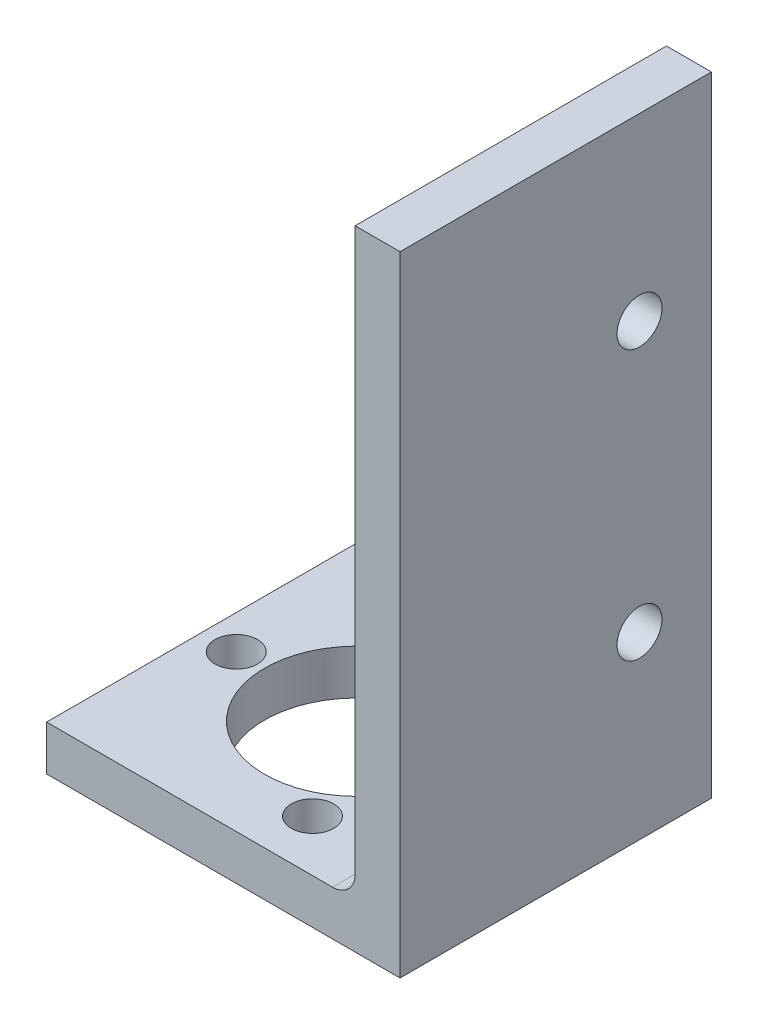
SolidWorks part; units mm, degrees
material "McMaster 6061-T6"
ref_plane "Front Plane" through (0, 0, 0) normal (0, 0, 1) x (1, 0, 0)
ref_plane "Top Plane" through (0, 0, 0) normal (0, 1, 0) x (1, 0, 0)
ref_plane "Right Plane" through (0, 0, 0) normal (1, 0, 0) x (0, 0, -1)
sketch "Sketch2" plane through (0, 0, 0) normal (0, 0, 1) x (1, 0, 0)
  line L0 (-25.4, 0) -> (25.4, 0)
  line L1 (25.4, 0) -> (25.4, 50.8)
  line L2 (25.4, 50.8) -> (22.225, 50.8)
  line L3 (22.225, 50.8) -> (22.225, 3.175)
  line L4 (22.225, 3.175) -> (-25.4, 3.175)
  line L5 (-25.4, 0) -> (-25.4, 3.175)
  line L6 (23.8125, 50.8) -> (25.4, 50.8) construction
  line L7 (-25.4, 1.5875) -> (-25.4, 0) construction
  dimension "Vert" = 50.8
  dimension "Horz" = 50.8
  dimension "Thickness" = 3.175
extrude "Boss-Extrude1" add sketch "Sketch2" along normal mid plane 22
fillet "Fillet1" radius 1.5875 1 edges at (22.225, 3.175, 0)
ref_plane "Contact Plane 1" through (0, 0, 0) normal (0, -1, 0) x (-1, 0, 0)
ref_plane "Contact Plane 2" through (25.4, 0, 0) normal (1, 0, 0) x (0, 0, -1)
ref_plane "Contact Plane 3" through (0, 3.175, 0) normal (0, 1, 0) x (1, 0, 0)
ref_plane "Contact Plane 4" through (22.225, 0, 0) normal (-1, 0, 0) x (0, 0, 1)
ref_plane "Contact Plane 5" through (0, 0, 11) normal (0, 0, 1) x (1, 0, 0)
ref_plane "Contact Plane 6" through (0, 0, -13.54) normal (0, 0, -1) x (-1, 0, 0)
sketch "Sketch3" plane through (0, 0, 11) normal (0, 0, 1) x (1, 0, 0)
  line L0 (-25.4, 0) -> (25.4, 0) construction
  line L1 (6.0591, 71.0024) -> (30.483, 71.0024)
  line L2 (6.0591, 71.0024) -> (6.0591, 44.45)
  line L3 (6.0591, 44.45) -> (30.483, 44.45)
  line L4 (30.483, 71.0024) -> (30.483, 44.45)
  dimension "D1" = 44.45
extrude "Cut-Extrude1" cut sketch "Sketch3" against normal through all
sketch "Sketch4" plane through (0, 0, 0) normal (0, -1, 0) x (1, 0, 0)
  line L0 (15.575, 7.3612) -> (15.575, -7.3612) construction
  line L1 (25.4, 11) -> (25.4, -11) construction
  line L2 (0.425, 11) -> (0.425, -11)
  line L3 (-25.4, 11) -> (25.4, 11) construction
  line L4 (-25.4, -11) -> (25.4, -11) construction
  circle A0 centre (11.325, 0) radius 6.5
  point P4 (15.575, 0)
  point P5 (25.4, 0)
  point P18 (11.325, 0)
  arc B0 (0.425, 0) -> (22.225, 0) centre (11.325, 0) ccw
  arc B1 (22.225, 0) -> (0.425, 0) centre (11.325, 0) ccw
  arc B2 (16.325, 8.6603) -> (14.825, 6.0622) centre (15.575, 7.3612) ccw
  arc B3 (14.825, 6.0622) -> (16.325, 8.6603) centre (15.575, 7.3612) ccw
  arc B4 (4.325, 0) -> (1.325, 0) centre (2.825, 0) ccw
  arc B5 (1.325, 0) -> (4.325, 0) centre (2.825, 0) ccw
  arc B6 (14.825, -6.0622) -> (16.325, -8.6603) centre (15.575, -7.3612) ccw
  arc B7 (16.325, -8.6603) -> (14.825, -6.0622) centre (15.575, -7.3612) ccw
  dimension "D1" = 13
sketch_block_instance "Block-MotorMounting-1"
sketch_block "Block-MotorMounting"
extrude "Cut-Extrude2" cut sketch "Sketch4" against normal through all
sketch "Sketch5" plane through (25.4, 0, 0) normal (1, 0, 0) x (0, 0, -1)
  line L0 (5.92, 44.45) -> (5.92, 31.75) construction
  line L2 (5.92, 31.75) -> (5.92, 12.7) construction
  line L3 (5.92, 12.7) -> (5.92, 0) construction
  line L6 (11, 44.45) -> (11, 4.7625) construction
  line L7 (-11, 0) -> (11, 0) construction
  line L9 (-11, 44.45) -> (11, 44.45) construction
  circle A1 centre (5.92, 31.75) radius 1.5875
  circle A2 centre (5.92, 12.7) radius 1.5875
  point P8 (0, 0)
  point P9 (0, 0)
  point P13 (0, 0)
  dimension "D1" = 3.175
  dimension "D2" = 12.7
  dimension "D3" = 5.08
extrude "Cut-Extrude3" cut sketch "Sketch5" against normal through all
equation "\"D1@Fillet1\"=\"Thickness@Sketch2\"/2"
